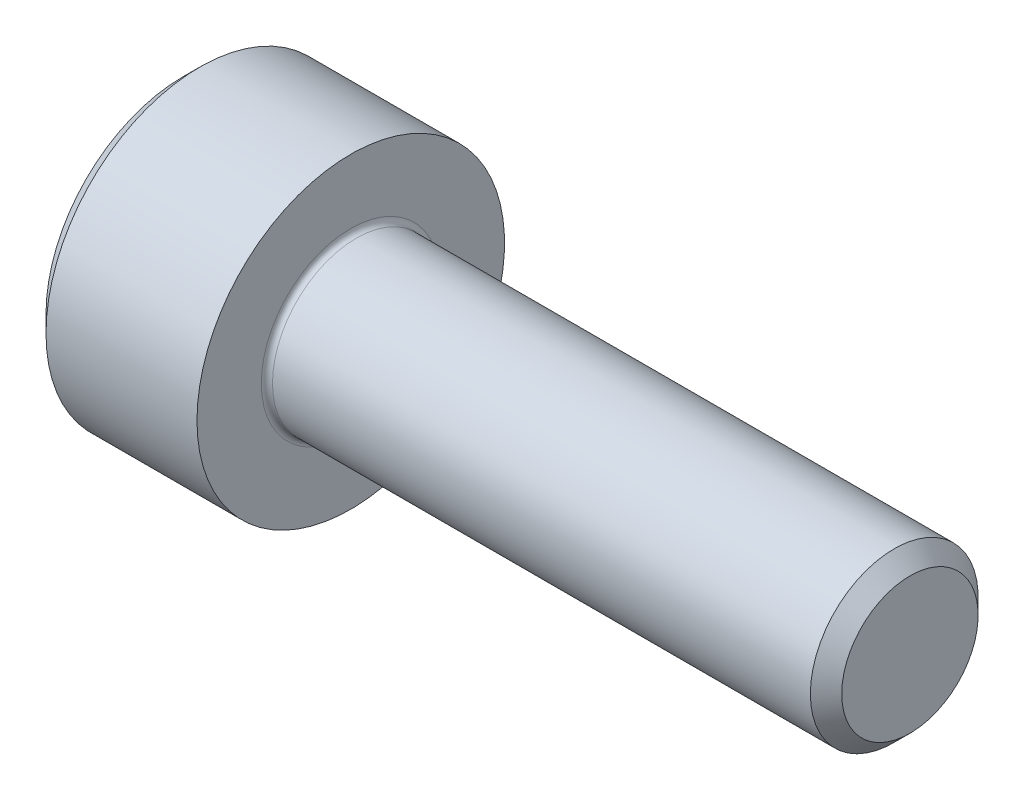
SolidWorks part; units mm, degrees
revolve "Base-Revolve" add sketch "BodySke"
sketch "BodySke" plane through (0, 0, 0) normal (0, 0, 1) x (1, 0, 0)
  line L0 (0, 0) -> (0, 2.45)
  line L1 (0.3, 2.75) -> (3, 2.75)
  line L2 (3, 2.75) -> (3, 1.5)
  line L3 (3, 1.5) -> (12.7195, 1.5)
  line L4 (13, 1.2195) -> (13, 0)
  line L5 (13, 0) -> (0, 0)
  line L6 (-31.75, 0) -> (127, 0) construction
  line L7 (0, 2.45) -> (0.3, 2.75)
  line L8 (13, 1.2195) -> (12.7195, 1.5)
  line L9 (0, -2.45) -> (0.3, -2.75) construction
  line L10 (13, -1.2195) -> (12.7195, -1.5) construction
  line L11 (3.5, 9.525) -> (3.5, 3.175) construction
  line L12 (-3, 9.525) -> (-3, 3.175) construction
  line L13 (-37, 9.525) -> (-37, 3.175) construction
  dimension "Diameter" = 3
  dimension "Head_ht" = 3
  dimension "Length" = 10
  dimension "Body_ch_ang" = 45
  dimension "Head_dia" = 5.5
  dimension "Head_ch_ang" = 45
  dimension "Minor_dia" = 2.439
  dimension "Advance" = 0.5
  dimension "Thread_nom" = 16
  dimension "Thread_length" = 50
  dimension "Head_ch_ht" = 0.3
cosmetic thread "ThreadCosmetic" [suppressed]
fillet "Fillet1" radius 0.1 1 edges at (3, 0, 1.5)
ref_plane "Plane1" through (0, 0, 0) normal (0, 0, 1) x (1, 0, 0)
ref_plane "Plane2" through (0, 0, 0) normal (0, 1, 0) x (1, 0, 0)
ref_plane "Plane3" through (0, 0, 0) normal (1, 0, 0) x (0, 0, -1)
sketch "Sketch2" plane through (0, 0, 0) normal (0, 0, 1) x (1, 0, 0)
  line L0 (0, 1.28) -> (1.3, 1.28)
  line L1 (1.3, 1.28) -> (2.039, 0)
  line L2 (-31.75, 0) -> (127, 0) construction
  line L3 (2.039, 0) -> (0, 0)
  line L4 (0, 0) -> (0, 1.28)
  line L5 (0, 2.45) -> (0, -2.45) construction
  line L6 (0, 0) -> (47.625, 0) construction
  line L7 (3, -2.75) -> (3, 2.75) construction
  dimension "D1" = 1.28
  dimension "D2" = 60
revolve "Hex-PreBroach" cut sketch "Sketch2" angle 360 about L6
sketch "Sketch3" plane through (0, 0, 0) normal (-1, 0, 0) x (0, 0.5, 0.866)
  line L0 (0.739, 1.28) -> (-0.739, 1.28)
  line L1 (-0.739, 1.28) -> (-1.478, 0)
  line L2 (0.739, 1.28) -> (1.478, 0)
  line L3 (0.739, -1.28) -> (1.478, 0)
  line L4 (0.739, -1.28) -> (-0.739, -1.28)
  line L5 (-0.739, -1.28) -> (-1.478, 0)
  dimension "D1" = 1.28
  dimension "D2" = 1.28
  dimension "Hex_size" = 2.56
extrude "Hex" cut sketch "Sketch3" against normal blind 1.3
sketch "Sketch4" plane through (0, 0, 0) normal (-1, 0, 0) x (0, 0, 1)
  line L0 (0, 0) -> (1.4605, 0)
  line L1 (0, 0) -> (6.1484, 3.5498) construction
  line L2 (0, 0) -> (0.7302, 1.2648)
  line L3 (1.2009, 0.3267) -> (1.3933, 0.4378)
  line L4 (0.8834, 0.8767) -> (1.0758, 0.9877)
  arc A0 (1.2009, 0.3267) -> (0.8834, 0.8767) centre (0, 0) ccw
  arc A1 (1.4605, 0) -> (1.3933, 0.4378) centre (0, 0) ccw
  arc A2 (0.7302, 1.2648) -> (1.0758, 0.9877) centre (0, 0) cw
  dimension "D1" = 30
  dimension "D2" = 60
  dimension "Spline_p_dim" = 0.635
  dimension "D3" = 0.3175
extrude "Spline" [suppressed] cut sketch "Sketch4" against normal blind 1.3
pattern_circular "CirPattern1" [suppressed] count 6 every 60
sketch "Sketch5" plane through (0, 0, 0) normal (0, 0, 1) x (1, 0, 0)
  line L0 (-31.75, 0) -> (127, 0) construction
  line L2 (0, 2.45) -> (0, -2.45) construction
  circle A0 centre (1.2, 0) radius 0.475
  dimension "Drilled_hole_dia" = 0.95
  dimension "Drilled_hole_loc" = 1.2
extrude "Hole" [suppressed] cut sketch "Sketch5" against normal through all and the other way through all
pattern_circular "Drilled-4" [suppressed] count 2 every 60
pattern_circular "Drilled-6" [suppressed] count 3 every 60
sketch "ThdSchSke" plane through (0, 0, 0) normal (0, 0, 1) x (1, 0, 0)
  line L0 (3.5, -1.2195) -> (3.3036, -1.5)
  line L1 (3.5, -1.2195) -> (3.6964, -1.5)
  line L2 (3.6964, -1.5) -> (3.6964, -1.875)
  line L3 (-3.175, 0) -> (5.1513, 0) construction
  line L5 (3.6964, -1.875) -> (3.3036, -1.875)
  line L6 (3.3036, -1.875) -> (3.3036, -1.5)
  line L7 (0, 2.45) -> (0, -2.45) construction
  dimension "Thread_minor" = 2.439
  dimension "Diameter" = 3
  dimension "Start" = 3.5
revolve "ThreadSchematic" [suppressed] cut sketch "ThdSchSke" angle 360 about L3
pattern_linear "ThdSchPat" [suppressed]
equation "\"D2@Sketch3\" = \"Hex_size@Sketch3\" / 2"
equation "\"D1@Sketch3\" = \"Hex_size@Sketch3\" / 2"
equation "\"D1@Sketch2\" = \"Hex_size@Sketch3\" / 2"
equation "\"D3@Sketch4\" = \"Spline_p_dim@Sketch4\" / 2"
equation "\"Thread_minor@ThreadCosmetic\"  =  \"Minor_dia@BodySke\""
equation "\"D2@CirPattern1\" = 360 / \"Num_teeth@CirPattern1\""
equation "\"Wall_thickness@Sketch2\" = \"Head_ht@BodySke\" - \"Key_eng@Hex\""
equation "\"Thread_length@ThreadCosmetic\" = ((sgn( (\"Length@BodySke\" - \"Advance@BodySke\" ) - \"Thread_nom@BodySke\" )-1)*( (\"Length@BodySke\" - \"Advance@BodySke\" ) - \"Thread_nom@BodySke\" ))/-2+ \"Thread_nom@BodySke\""
equation "\"Thread_minor@ThdSchSke\" = \"Minor_dia@BodySke\""
equation "\"Diameter@ThdSchSke\" = \"Diameter@BodySke\""
equation "\"Overcut@ThdSchSke\" = \"Diameter@BodySke\" * 1.25"
equation "\"Start@ThdSchSke\" = \"Head_ht@BodySke\" + \"Length@BodySke\" - \"Thread_length@ThreadCosmetic\"  '---Non-countersunk---"
equation "\"Num_threads@ThdSchPat\" = int( \"Thread_length@ThreadCosmetic\" / \"Advance@BodySke\" + 0.999 )  + 1"
equation "\"Advance@ThdSchPat\" = \"Thread_length@ThreadCosmetic\" /  (\"Num_threads@ThdSchPat\" - 1) 'relax it"
equation "\"Num_threads@ThdSchPat\" = \"Num_threads@ThdSchPat\" - sgn( \"Num_threads@ThdSchPat\" - 1) '---chamfered tips only---"
